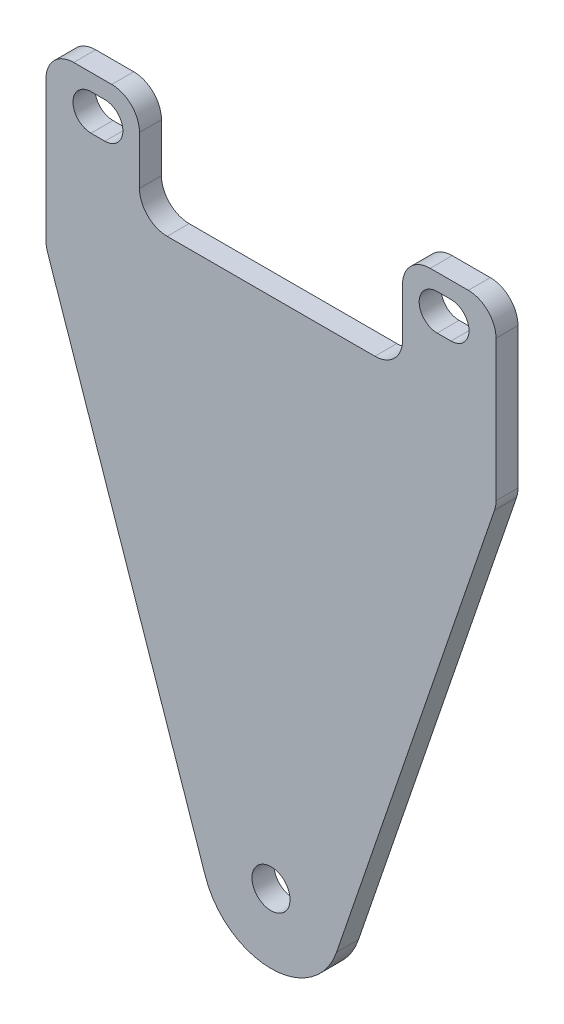
SolidWorks part; units mm, degrees
ref_plane "Front Plane" through (0, 0, 0) normal (0, 0, 1) x (1, 0, 0)
ref_plane "Top Plane" through (0, 0, 0) normal (0, 1, 0) x (1, 0, 0)
ref_plane "Right Plane" through (0, 0, 0) normal (1, 0, 0) x (0, 0, -1)
sketch "Sketch1" plane through (0, 0, 0) normal (0, 0, 1) x (1, 0, 0)
  line L0 (0, 0) -> (0, 120) construction
  line L1 (32.5, 120) -> (-32.5, 120)
  line L2 (-32.5, 120) -> (-32.5, 95)
  line L3 (-32.5, 95) -> (0, 0)
  line L4 (32.5, 95) -> (0, 0)
  line L5 (32.5, 120) -> (32.5, 95)
  dimension "D1" = 65
  dimension "D2" = 25
  dimension "D3" = 120
extrude "Boss-Extrude1" add sketch "Sketch1" along normal blind 3.175
sketch "Sketch2" plane through (0, 0, 3.175) normal (0, 0, 1) x (1, 0, 0)
  line L0 (0, 120) -> (0, 105) construction
  line L1 (32.5, 120) -> (-32.5, 120) construction
  line L2 (-26, 115) -> (-24, 115) construction
  line L3 (-19, 120) -> (19, 120)
  line L4 (-19, 120) -> (-19, 105)
  line L5 (-19, 105) -> (19, 105)
  line L6 (19, 120) -> (19, 105)
  line L7 (-26, 117.6) -> (-24, 117.6)
  line L8 (-26, 112.4) -> (-24, 112.4)
  line L9 (26, 115) -> (24, 115) construction
  line L10 (26, 117.6) -> (24, 117.6)
  line L11 (26, 112.4) -> (24, 112.4)
  arc A0 (-26, 117.6) -> (-26, 112.4) centre (-26, 115) ccw
  arc A1 (-24, 112.4) -> (-24, 117.6) centre (-24, 115) ccw
  arc A2 (26, 117.6) -> (26, 112.4) centre (26, 115) cw
  arc A3 (24, 112.4) -> (24, 117.6) centre (24, 115) cw
  point P9 (-25, 115)
  point P18 (25, 115)
  dimension "D5" = 2.6
  dimension "D1" = 15
  dimension "D2" = 38
  dimension "D3" = 50
  dimension "D4" = 2
  dimension "D6" = 5
extrude "Cut-Extrude1" cut sketch "Sketch2" against normal through all
fillet "Fillet1" radius 4 8 edges at (32.5, 95, 1.5875) (32.5, 120, 1.5875) (19, 120, 1.5875) (19, 105, 1.5875) (-19, 105, 1.5875) (-32.5, 95, 1.5875) (-32.5, 120, 1.5875) (-19, 120, 1.5875)
fillet "Fillet2" radius 10 1 edges at (0, 0, 1.5875)
sketch "Sketch3" plane through (0, 0, 3.175) normal (0, 0, 1) x (1, 0, 0)
  circle A0 centre (0, 30.894) radius 2.75
  dimension "D1" = 5.5
extrude "Cut-Extrude2" cut sketch "Sketch3" against normal through all
